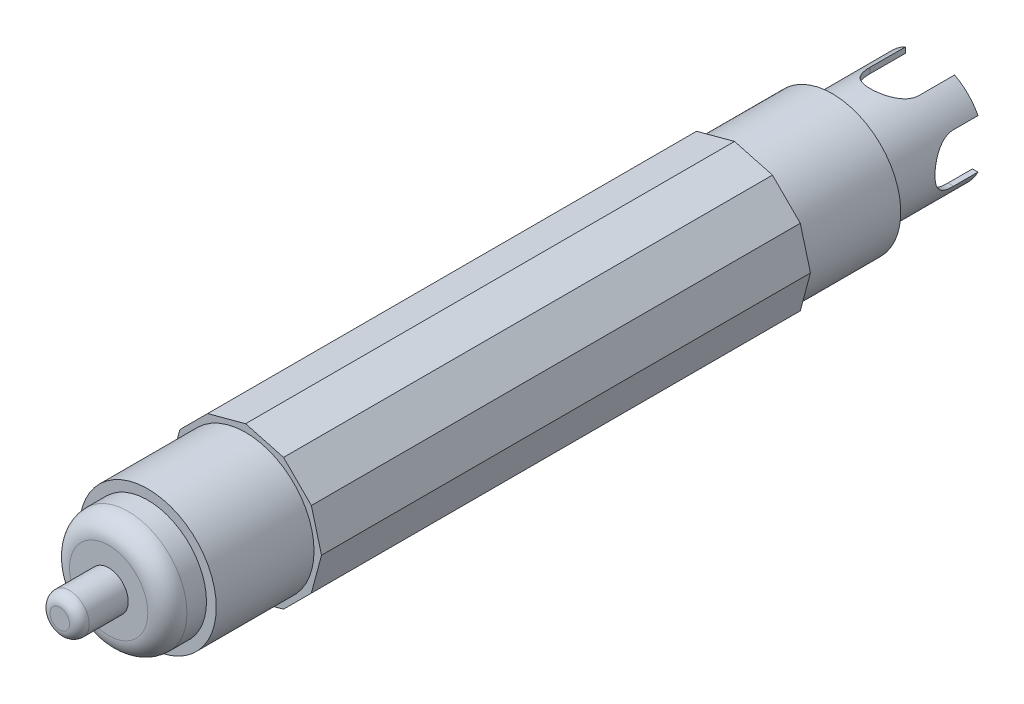
SolidWorks part; units mm, degrees
ref_plane "Front Plane" through (0, 0, 0) normal (0, 0, 1) x (1, 0, 0)
ref_plane "Top Plane" through (0, 0, 0) normal (0, 1, 0) x (1, 0, 0)
ref_plane "Right Plane" through (0, 0, 0) normal (1, 0, 0) x (0, 0, -1)
sketch "Sketch1" plane through (0, 0, 0) normal (0, 0, 1) x (1, 0, 0)
  line L0 (-15.5291, 0) -> (-13.4486, -7.7646)
  line L1 (15.5291, 0) -> (13.4486, 7.7646)
  line L2 (13.4486, 7.7646) -> (7.7646, 13.4486)
  line L3 (7.7646, 13.4486) -> (0, 15.5291)
  line L4 (0, 15.5291) -> (-7.7646, 13.4486)
  line L5 (-7.7646, 13.4486) -> (-13.4486, 7.7646)
  line L6 (-13.4486, 7.7646) -> (-15.5291, 0)
  line L7 (-13.4486, -7.7646) -> (-7.7646, -13.4486)
  line L8 (-7.7646, -13.4486) -> (0, -15.5291)
  line L9 (0, -15.5291) -> (7.7646, -13.4486)
  line L10 (7.7646, -13.4486) -> (13.4486, -7.7646)
  line L11 (13.4486, -7.7646) -> (15.5291, 0)
  circle A0 centre (0, 0) radius 15 construction
extrude "Boss-Extrude1" add sketch "Sketch1" against normal blind 100
sketch "Sketch2" plane through (0, 0, 0) normal (0, 0, 1) x (1, 0, 0)
  circle A0 centre (0, 0) radius 14
  dimension "D1" = 28
extrude "Boss-Extrude2" add sketch "Sketch2" along normal blind 20
sketch "Sketch3" plane through (0, 0, 20) normal (0, 0, 1) x (1, 0, 0)
  circle A0 centre (0, 0) radius 12
extrude "Boss-Extrude3" add sketch "Sketch3" along normal blind 8
fillet "Fillet1" radius 4 1 edges at (12, 0, 28)
sketch "Sketch4" plane through (0, 0, 28) normal (0, 0, 1) x (1, 0, 0)
  circle A0 centre (0, 0) radius 4
extrude "Boss-Extrude4" add sketch "Sketch4" along normal blind 10
fillet "Fillet2" radius 2 1 edges at (4, 0, 38)
sketch "Sketch6" plane through (0, 0, -100) normal (0, 0, -1) x (-1, 0, 0)
  circle A0 centre (0, 0) radius 14
extrude "Boss-Extrude6" add sketch "Sketch6" along normal blind 20
sketch "Sketch7" plane through (0, 0, -120) normal (0, 0, -1) x (-1, 0, 0)
  circle A0 centre (0, 0) radius 10
  circle A1 centre (0, 0) radius 11
  dimension "D1" = 1
extrude "Boss-Extrude7" add sketch "Sketch7" along normal blind 20
sketch "Sketch8" plane through (0, 0, 0) normal (1, 0, 0) x (0, 0, -1)
  line L0 (140, -11) -> (140, 11) construction
  line L1 (145, -5) -> (135, -5)
  line L2 (145, -5) -> (145, 5)
  line L3 (145, 5) -> (135, 5)
  line L5 (145, -5) -> (135, 5) construction
  line L6 (145, 5) -> (135, -5) construction
  arc A0 (135, 5) -> (135, -5) centre (135, 0) ccw
  point P0 (140, 0)
  dimension "D1" = 10
extrude "Cut-Extrude1" cut sketch "Sketch8" against normal up to next and the other way up to next
sketch "Sketch9" plane through (0, 0, 0) normal (0, 1, 0) x (1, 0, 0)
  line L0 (9.798, 140) -> (-9.798, 140) construction
  line L2 (-5, 132.7558) -> (-5, 147.2442)
  line L3 (-5, 147.2442) -> (5, 147.2442)
  line L4 (5, 132.7558) -> (5, 147.2442)
  line L5 (-5, 132.7558) -> (5, 147.2442) construction
  line L6 (-5, 147.2442) -> (5, 132.7558) construction
  arc A0 (-5, 132.7558) -> (5, 132.7558) centre (0, 132.7558) ccw
  point P0 (0, 140)
  dimension "D1" = 10
extrude "Cut-Extrude2" cut sketch "Sketch9" against normal up to next and the other way up to next
sketch "Sketch10" plane through (0, 0, -120) normal (0, 0, -1) x (-1, 0, 0)
  circle A0 centre (0, 0) radius 10
extrude "Boss-Extrude8" add sketch "Sketch10" along normal blind 8
sketch "Sketch11" plane through (0, 0, -128) normal (0, 0, -1) x (-1, 0, 0)
  circle A0 centre (0, 0) radius 3
extrude "Boss-Extrude9" add sketch "Sketch11" along normal blind 6
fillet "Fillet3" radius 3 1 edges at (-3, 0, -134)
